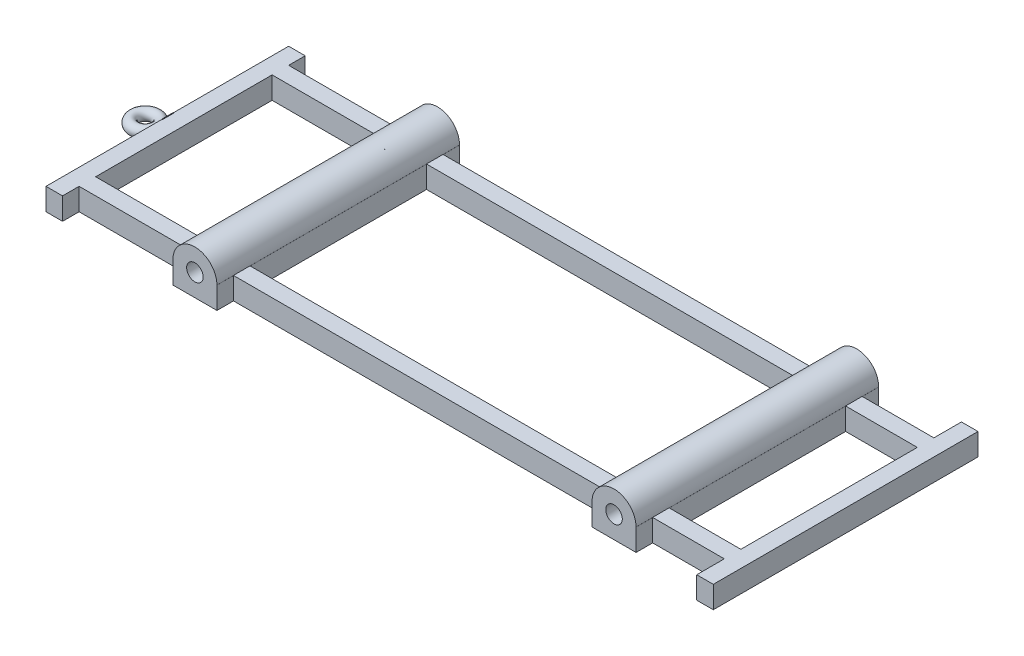
SolidWorks part; units mm, degrees
ref_plane "Front Plane" through (0, 0, 0) normal (0, 0, 1) x (1, 0, 0)
ref_plane "Top Plane" through (0, 0, 0) normal (0, 1, 0) x (1, 0, 0)
ref_plane "Right Plane" through (0, 0, 0) normal (1, 0, 0) x (0, 0, -1)
sketch "Sketch1" plane through (0, 0, 0) normal (0, 1, 0) x (1, 0, 0)
  line L0 (-207.0139, 0) -> (209.6875, 0) construction
  line L2 (-207.0139, 110) -> (-192.0139, 110)
  line L3 (-207.0139, 110) -> (-207.0139, -110)
  line L4 (-207.0139, -110) -> (-192.0139, -110)
  line L5 (-192.0139, 110) -> (-192.0139, -110)
  line L6 (407.9861, 120) -> (392.9861, 120)
  line L7 (407.9861, 120) -> (407.9861, -120)
  line L8 (407.9861, -120) -> (392.9861, -120)
  line L9 (392.9861, 120) -> (392.9861, -120)
  line L10 (392.9861, -95) -> (-192.0139, -95)
  line L11 (392.9861, -95) -> (392.9861, -80)
  line L12 (392.9861, -80) -> (-192.0139, -80)
  line L13 (-192.0139, -95) -> (-192.0139, -80)
  line L14 (-192.0139, 80) -> (392.9861, 80)
  line L15 (-192.0139, 80) -> (-192.0139, 95)
  line L16 (-192.0139, 95) -> (392.9861, 95)
  line L17 (392.9861, 80) -> (392.9861, 95)
  dimension "D1" = 220
  dimension "D2" = 110
  dimension "D3" = 240
  dimension "D4" = 120
  dimension "D5" = 615
  dimension "D6" = 15
  dimension "D7" = 80
  dimension "D8" = 80
  dimension "D9" = 15
  dimension "D10" = 15
  dimension "D11" = 15
extrude "Boss-Extrude1" add sketch "Sketch1" along normal blind 20 contours L9 L12 L5 L10 | L16 L17 L14 L15
sketch "Sketch2" plane through (0, 0, 0) normal (0, 0, 1) x (1, 0, 0)
  line L0 (327.9298, 19.9436) -> (327.9861, 19.9436)
  line L1 (-92.0139, 0) -> (-52.0139, 0)
  line L2 (-92.0139, 0) -> (-92.0139, 19.9436)
  line L3 (-92.0139, 19.9436) -> (-91.9575, 19.9436)
  line L4 (-52.0139, 0) -> (-52.0139, 19.9436)
  line L5 (287.9861, 0) -> (327.9861, 0)
  line L6 (287.9861, 0) -> (287.9861, 19.9436)
  line L7 (287.9861, 19.9436) -> (288.0425, 19.9436)
  line L8 (327.9861, 0) -> (327.9861, 19.9436)
  line L9 (-52.0702, 19.9436) -> (-52.0139, 19.9436)
  line L10 (-207.0139, 20) -> (-207.0139, 0) construction
  line L11 (407.9861, 20) -> (407.9861, 0) construction
  arc A0 (327.9298, 19.9436) -> (288.0425, 19.9436) centre (307.9861, 19.9436) ccw
  arc A1 (-52.0702, 19.9436) -> (-91.9575, 19.9436) centre (-72.0139, 19.9436) ccw
  dimension "D1" = 40
  dimension "D2" = 40
  dimension "D3" = 135
  dimension "D4" = 100
extrude "Boss-Extrude2" add sketch "Sketch2" along normal mid plane 220
sketch "Sketch3" plane through (0, 0, -110) normal (0, 0, -1) x (-1, 0, 0)
  circle A0 centre (72.0139, 19.9436) radius 7.5
  circle A1 centre (-307.9861, 19.9436) radius 7.5
  dimension "D1" = 15
  dimension "D2" = 15
extrude "Cut-Extrude1" cut sketch "Sketch3" against normal through all
sketch "Sketch4" plane through (0, 0, 0) normal (0, 0, 1) x (1, 0, 0)
  line L0 (406.9666, 0.9629) -> (449.0057, 0.9629) construction
  line L1 (449.0057, 0.9629) -> (427.9861, 0.9629) construction
  line L2 (427.9861, 0.9629) -> (427.9861, 16.8177) construction
  circle A0 centre (437.9861, 5.9629) radius 5
  dimension "D1" = 10
  dimension "D2" = 10
  dimension "D3" = 20
sketch "Sketch7" plane through (0, 0, 0) normal (0, -1, 0) x (-1, 0, 0)
  line L0 (207.0139, 0) -> (-624.2965, 0) construction
  line L1 (207.0139, 110) -> (207.0139, -110) construction
  line L2 (72.0139, 30) -> (72.0139, -30) construction
  line L5 (77.0139, 30) -> (77.0139, -30)
  line L8 (416.5173, 0) -> (-523.0163, 0) construction
  line L10 (67.0139, 30) -> (67.0139, -30)
  line L11 (-307.9861, 30) -> (-307.9861, -30) construction
  line L12 (-302.9861, 30) -> (-302.9861, -30)
  line L13 (-312.9861, 30) -> (-312.9861, -30)
  arc A4 (77.0139, 30) -> (67.0139, 30) centre (72.0139, 30) ccw
  arc A5 (67.0139, -30) -> (77.0139, -30) centre (72.0139, -30) ccw
  arc A6 (-302.9861, 30) -> (-312.9861, 30) centre (-307.9861, 30) ccw
  arc A7 (-312.9861, -30) -> (-302.9861, -30) centre (-307.9861, -30) ccw
  point P7 (72.0139, 0)
  point P13 (-307.9861, 0)
  dimension "D3" = 5
  dimension "D4" = 5
  dimension "D1" = 60
  dimension "D2" = 60
  dimension "D5" = 380
  dimension "D6" = 135
sketch "Sketch9" plane through (0, 0, 0) normal (0, 0, 1) x (1, 0, 0)
  line L0 (-416.5173, 0) -> (624.2965, 0) construction
  line L1 (-227.0139, 0) -> (-227.0139, 20) construction
  circle A0 centre (-237.0139, 5) radius 5
  dimension "D1" = 10
  dimension "D2" = 10
  dimension "D3" = 20
  dimension "D4" = 20
revolve "Revolve1" add sketch "Sketch9" angle 360 about L1
sketch "Sketch12" plane through (0, 0, 0) normal (0, 0, 1) x (1, 0, 0)
  line L0 (-416.5173, 0) -> (418.5943, 0.9629) construction
  line L1 (406.9666, 0.9629) -> (449.0057, 0.9629) construction
  line L2 (-206.542, 0.2421) -> (-216.88, 0.2302)
  line L3 (-216.88, 0.2302) -> (-206.5656, 20.7216)
  line L4 (-206.5656, 20.7216) -> (-206.542, 0.2421)
extrude "Boss-Extrude3" add sketch "Sketch12" along normal mid plane 10
extrude "Boss-Extrude4" add sketch "Sketch7" along normal blind 10
